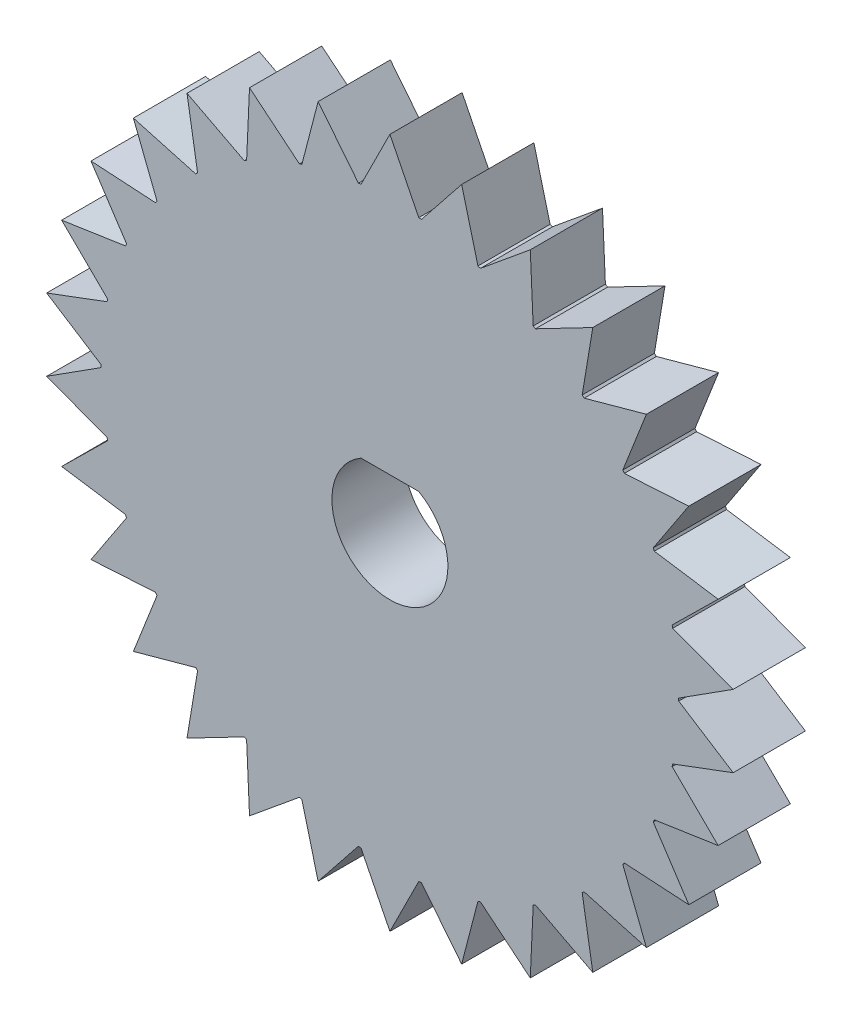
SolidWorks part; units mm, degrees
ref_plane "Front Plane" through (0, 0, 0) normal (0, 0, 1) x (1, 0, 0)
ref_plane "Top Plane" through (0, 0, 0) normal (0, 1, 0) x (1, 0, 0)
ref_plane "Right Plane" through (0, 0, 0) normal (1, 0, 0) x (0, 0, -1)
sketch "Sketch1" plane through (0, 0, 0) normal (0, 0, 1) x (1, 0, 0)
  line L1 (1.27, 12.6363) -> (0, 15.1763)
  line L2 (0, 15.1763) -> (-1.27, 12.6363)
  line L3 (0, 15.1763) -> (0, 0) construction
  line L4 (3.1553, 14.8447) -> (1.385, 12.6243)
  line L5 (3.8695, 12.0962) -> (3.1553, 14.8447)
  line L6 (6.1728, 13.8643) -> (3.9795, 12.0604)
  line L7 (6.2999, 11.0273) -> (6.1728, 13.8643)
  line L8 (8.9204, 12.2779) -> (6.4, 10.9695)
  line L9 (8.4549, 9.4765) -> (8.9204, 12.2779)
  line L10 (11.2782, 10.155) -> (8.5408, 9.3992)
  line L11 (10.2404, 7.5116) -> (11.2782, 10.155)
  line L12 (13.1431, 7.5882) -> (10.3084, 7.418)
  line L13 (11.5784, 5.2183) -> (13.1431, 7.5882)
  line L14 (14.4336, 4.6897) -> (11.6254, 5.1127)
  line L15 (12.4103, 2.697) -> (14.4336, 4.6897)
  line L16 (15.0932, 1.5864) -> (12.4344, 2.5839)
  line L17 (12.6999, 0.0578) -> (15.0932, 1.5864)
  line L18 (15.0932, -1.5864) -> (12.6999, -0.0578)
  line L19 (12.4344, -2.5839) -> (15.0932, -1.5864)
  line L20 (14.4336, -4.6897) -> (12.4103, -2.697)
  line L21 (11.6254, -5.1127) -> (14.4336, -4.6897)
  line L22 (13.1431, -7.5882) -> (11.5784, -5.2183)
  line L23 (10.3084, -7.418) -> (13.1431, -7.5882)
  line L24 (11.2782, -10.155) -> (10.2404, -7.5116)
  line L25 (8.5408, -9.3992) -> (11.2782, -10.155)
  line L26 (8.9204, -12.2779) -> (8.4549, -9.4765)
  line L27 (6.4, -10.9695) -> (8.9204, -12.2779)
  line L28 (6.1728, -13.8643) -> (6.2999, -11.0273)
  line L29 (3.9795, -12.0604) -> (6.1728, -13.8643)
  line L30 (3.1553, -14.8447) -> (3.8695, -12.0962)
  line L31 (1.385, -12.6243) -> (3.1553, -14.8447)
  line L32 (0, -15.1763) -> (1.27, -12.6363)
  line L33 (-1.27, -12.6363) -> (0, -15.1763)
  line L34 (-3.1553, -14.8447) -> (-1.385, -12.6243)
  line L35 (-3.8695, -12.0962) -> (-3.1553, -14.8447)
  line L36 (-6.1728, -13.8643) -> (-3.9795, -12.0604)
  line L37 (-6.2999, -11.0273) -> (-6.1728, -13.8643)
  line L38 (-8.9204, -12.2779) -> (-6.4, -10.9695)
  line L39 (-8.4549, -9.4765) -> (-8.9204, -12.2779)
  line L40 (-11.2782, -10.155) -> (-8.5408, -9.3992)
  line L41 (-10.2404, -7.5116) -> (-11.2782, -10.155)
  line L42 (-13.1431, -7.5882) -> (-10.3084, -7.418)
  line L43 (-11.5784, -5.2183) -> (-13.1431, -7.5882)
  line L44 (-14.4336, -4.6897) -> (-11.6254, -5.1127)
  line L45 (-12.4103, -2.697) -> (-14.4336, -4.6897)
  line L46 (-15.0932, -1.5864) -> (-12.4344, -2.5839)
  line L47 (-12.6999, -0.0578) -> (-15.0932, -1.5864)
  line L48 (-15.0932, 1.5864) -> (-12.6999, 0.0578)
  line L49 (-12.4344, 2.5839) -> (-15.0932, 1.5864)
  line L50 (-14.4336, 4.6897) -> (-12.4103, 2.697)
  line L51 (-11.6254, 5.1127) -> (-14.4336, 4.6897)
  line L52 (-13.1431, 7.5882) -> (-11.5784, 5.2183)
  line L53 (-10.3084, 7.418) -> (-13.1431, 7.5882)
  line L54 (-11.2782, 10.155) -> (-10.2404, 7.5116)
  line L55 (-8.5408, 9.3992) -> (-11.2782, 10.155)
  line L56 (-8.9204, 12.2779) -> (-8.4549, 9.4765)
  line L57 (-6.4, 10.9695) -> (-8.9204, 12.2779)
  line L58 (-6.1728, 13.8643) -> (-6.2999, 11.0273)
  line L59 (-3.9795, 12.0604) -> (-6.1728, 13.8643)
  line L60 (-3.1553, 14.8447) -> (-3.8695, 12.0962)
  line L61 (-1.385, 12.6243) -> (-3.1553, 14.8447)
  arc A0 (-1.27, 12.6363) -> (-1.385, 12.6243) centre (0, 0) ccw
  arc A1 (-3.8695, 12.0962) -> (-3.9795, 12.0604) centre (0, 0) ccw
  arc A2 (-6.2999, 11.0273) -> (-6.4, 10.9695) centre (0, 0) ccw
  arc A3 (-8.4549, 9.4765) -> (-8.5408, 9.3992) centre (0, 0) ccw
  arc A4 (-10.2404, 7.5116) -> (-10.3084, 7.418) centre (0, 0) ccw
  arc A5 (-11.5784, 5.2183) -> (-11.6254, 5.1127) centre (0, 0) ccw
  arc A6 (-12.4103, 2.697) -> (-12.4344, 2.5839) centre (0, 0) ccw
  arc A7 (-12.6999, 0.0578) -> (-12.6999, -0.0578) centre (0, 0) ccw
  arc A8 (-12.4344, -2.5839) -> (-12.4103, -2.697) centre (0, 0) ccw
  arc A9 (-11.6254, -5.1127) -> (-11.5784, -5.2183) centre (0, 0) ccw
  arc A10 (-10.3084, -7.418) -> (-10.2404, -7.5116) centre (0, 0) ccw
  arc A11 (-8.5408, -9.3992) -> (-8.4549, -9.4765) centre (0, 0) ccw
  arc A12 (-6.4, -10.9695) -> (-6.2999, -11.0273) centre (0, 0) ccw
  arc A13 (-3.9795, -12.0604) -> (-3.8695, -12.0962) centre (0, 0) ccw
  arc A14 (-1.385, -12.6243) -> (-1.27, -12.6363) centre (0, 0) ccw
  arc A15 (1.27, -12.6363) -> (1.385, -12.6243) centre (0, 0) ccw
  arc A16 (3.8695, -12.0962) -> (3.9795, -12.0604) centre (0, 0) ccw
  arc A17 (6.2999, -11.0273) -> (6.4, -10.9695) centre (0, 0) ccw
  arc A18 (8.4549, -9.4765) -> (8.5408, -9.3992) centre (0, 0) ccw
  arc A19 (10.2404, -7.5116) -> (10.3084, -7.418) centre (0, 0) ccw
  arc A20 (11.5784, -5.2183) -> (11.6254, -5.1127) centre (0, 0) ccw
  arc A21 (12.4103, -2.697) -> (12.4344, -2.5839) centre (0, 0) ccw
  arc A22 (12.6999, -0.0578) -> (12.6999, 0.0578) centre (0, 0) ccw
  arc A23 (12.4344, 2.5839) -> (12.4103, 2.697) centre (0, 0) ccw
  arc A24 (11.6254, 5.1127) -> (11.5784, 5.2183) centre (0, 0) ccw
  arc A25 (10.3084, 7.418) -> (10.2404, 7.5116) centre (0, 0) ccw
  arc A26 (8.5408, 9.3992) -> (8.4549, 9.4765) centre (0, 0) ccw
  arc A27 (6.4, 10.9695) -> (6.2999, 11.0273) centre (0, 0) ccw
  arc A28 (3.9795, 12.0604) -> (3.8695, 12.0962) centre (0, 0) ccw
  arc A29 (1.385, 12.6243) -> (1.27, 12.6363) centre (0, 0) ccw
  circle A30 centre (0, 0) radius 12.7 construction
  dimension "D1" = 2.54
  dimension "D4" = 30
extrude "Boss-Extrude1" add sketch "Sketch1" along normal blind 3.175
sketch "Sketch2" plane through (0, 0, 3.175) normal (0, 0, 1) x (1, 0, 0)
  circle A0 centre (0, 0) radius 2.55
  dimension "D1" = 5.1
extrude "Cut-Extrude1" cut sketch "Sketch2" against normal through all
sketch "Sketch3" plane through (0, 0, 3.175) normal (0, 0, 1) x (1, 0, 0)
  line L0 (-1.27, 2.2112) -> (1.27, 2.2112)
  circle A0 centre (0, 0) radius 2.55 construction
  arc A1 (1.27, 2.2112) -> (-1.27, 2.2112) centre (0, 0) ccw
  dimension "D1" = 2.54
extrude "Boss-Extrude2" add sketch "Sketch3" against normal through all
